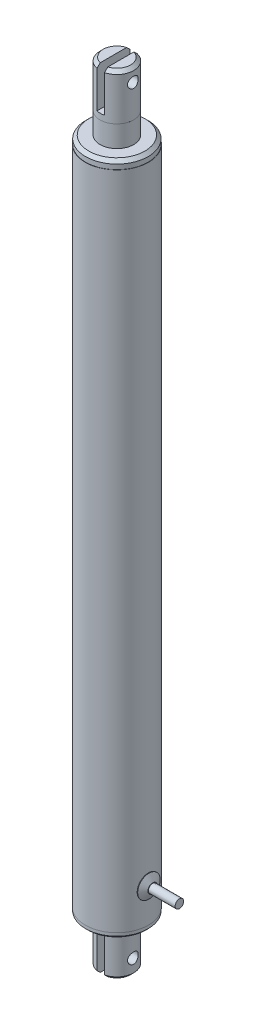
SolidWorks part; units mm, degrees
ref_plane "Front Plane" through (0, 0, 0) normal (0, 0, 1) x (1, 0, 0)
ref_plane "Top Plane" through (0, 0, 0) normal (0, 1, 0) x (1, 0, 0)
ref_plane "Right Plane" through (0, 0, 0) normal (1, 0, 0) x (0, 0, -1)
sketch "Sketch1" plane through (0, 0, 0) normal (0, 1, 0) x (1, 0, 0)
  circle A0 centre (0, 0) radius 14.986
  dimension "D1" = 29.972
extrude "Boss-Extrude1" add sketch "Sketch1" along normal blind 313.944
sketch "Sketch2" plane through (0, 0, 0) normal (0, -1, 0) x (1, 0, 0)
  circle A0 centre (0, 0) radius 14.859
  dimension "D1" = 29.718
extrude "Boss-Extrude2" add sketch "Sketch2" along normal blind 2.54
chamfer "Chamfer1" distance 1.016 angle 45 1 edges at (0, -2.54, -14.859)
sketch "Sketch3" plane through (0, -2.54, 0) normal (0, -1, 0) x (1, 0, 0)
  circle A0 centre (0, 0) radius 8.001
  dimension "D1" = 16.002
extrude "Boss-Extrude3" add sketch "Sketch3" along normal blind 22.098
chamfer "Chamfer2" distance 1.524 angle 45 1 edges at (0, -24.638, -8.001)
ref_plane "Plane1" through (-8.001, 0, 0) normal (-1, 0, 0) x (0, 0, 1)
sketch "Sketch4" plane through (-8.001, 0, 0) normal (-1, 0, 0) x (0, 0, 1)
  line L0 (-6.477, -24.638) -> (6.477, -24.638) construction
  circle A0 centre (0, -17.018) radius 2.54
  dimension "D1" = 5.08
  dimension "D2" = 7.62
extrude "Cut-Extrude1" cut sketch "Sketch4" against normal blind 21.59
ref_plane "Plane2" through (0, 0, -8.001) normal (0, 0, -1) x (-1, 0, 0)
sketch "Sketch5" plane through (0, 0, -8.001) normal (0, 0, -1) x (-1, 0, 0)
  line L0 (-8.001, -19.558) -> (-8.001, -23.114) construction
  line L1 (1.651, -28.9772) -> (-1.905, -28.9772)
  line L2 (1.651, -28.9772) -> (1.651, -6.096)
  line L3 (1.651, -6.096) -> (-1.905, -6.096)
  line L4 (-1.905, -28.9772) -> (-1.905, -6.096)
  line L7 (-6.477, -24.638) -> (6.477, -24.638) construction
  dimension "D1" = 3.556
  dimension "D2" = 6.096
  dimension "D3" = 18.542
extrude "Cut-Extrude2" cut sketch "Sketch5" against normal blind 21.59
ref_plane "Plane3" through (14.986, 0, 0) normal (1, 0, 0) x (0, 0, -1)
sketch "Sketch6" plane through (14.986, 0, 0) normal (1, 0, 0) x (0, 0, -1)
  circle A0 centre (0, 16.2013) radius 5.334
  dimension "D1" = 10.668
extrude "Boss-Extrude4" add sketch "Sketch6" along normal blind 2.032 separate body contours A0
chamfer "Chamfer3" distance 1.778 angle 60 1 edges at (17.018, 16.2013, -5.334)
sketch "Sketch7" plane through (17.018, 0, 0) normal (1, 0, 0) x (0, 0, -1)
  circle A0 centre (0, 16.2013) radius 2.032
  dimension "D1" = 4.064
extrude "Boss-Extrude5" add sketch "Sketch7" along normal blind 12.7 contours A0
sketch "Sketch8" plane through (0, 313.944, 0) normal (0, 1, 0) x (1, 0, 0)
  circle A0 centre (0, 0) radius 14.859
  dimension "D1" = 29.718
extrude "Boss-Extrude6" add sketch "Sketch8" along normal blind 3.81
chamfer "Chamfer4" distance 1.524 angle 45 1 edges at (0, 317.754, 14.859)
sketch "Sketch9" plane through (0, 317.754, 0) normal (0, 1, 0) x (1, 0, 0)
  circle A0 centre (0, 0) radius 8.001
  dimension "D1" = 16.002
extrude "Boss-Extrude7" add sketch "Sketch9" along normal blind 10.16
sketch "Sketch10" plane through (0, 327.914, 0) normal (0, 1, 0) x (1, 0, 0)
  circle A0 centre (0, 0) radius 8.001
extrude "Boss-Extrude8" add sketch "Sketch10" along normal blind 21.844 separate body
chamfer "Chamfer5" distance 1.524 angle 45 1 edges at (0, 349.758, 8.001)
ref_plane "Plane4" through (-8.001, 0, 0) normal (-1, 0, 0) x (0, 0, 1)
sketch "Sketch11" plane through (-8.001, 0, 0) normal (-1, 0, 0) x (0, 0, 1)
  line L0 (6.477, 349.758) -> (-6.477, 349.758) construction
  circle A0 centre (0, 343.408) radius 2.54
  dimension "D1" = 5.08
  dimension "D2" = 6.35
extrude "Cut-Extrude3" cut sketch "Sketch11" against normal blind 21.844
ref_plane "Plane5" through (0, 0, -8.001) normal (0, 0, -1) x (-1, 0, 0)
sketch "Sketch12" plane through (0, 0, -8.001) normal (0, 0, -1) x (-1, 0, 0)
  line L0 (-8.001, 340.868) -> (-8.001, 327.914) construction
  line L1 (-1.905, 330.708) -> (1.651, 330.708)
  line L2 (-1.905, 330.708) -> (-1.905, 349.758)
  line L3 (-1.905, 349.758) -> (1.651, 349.758)
  line L4 (1.651, 330.708) -> (1.651, 349.758)
  line L5 (6.477, 349.758) -> (-6.477, 349.758) construction
  point P8 (-0.127, 330.708)
  dimension "D1" = 6.096
  dimension "D2" = 3.556
  dimension "D3" = 0
  dimension "D4" = 19.05
extrude "Cut-Extrude4" cut sketch "Sketch12" against normal blind 21.844 contours L4 L3 L2 L1
equation "\"stroke\"= 6"
equation "\"D1@Boss-Extrude1\"= \"stroke\" + 6.36"
